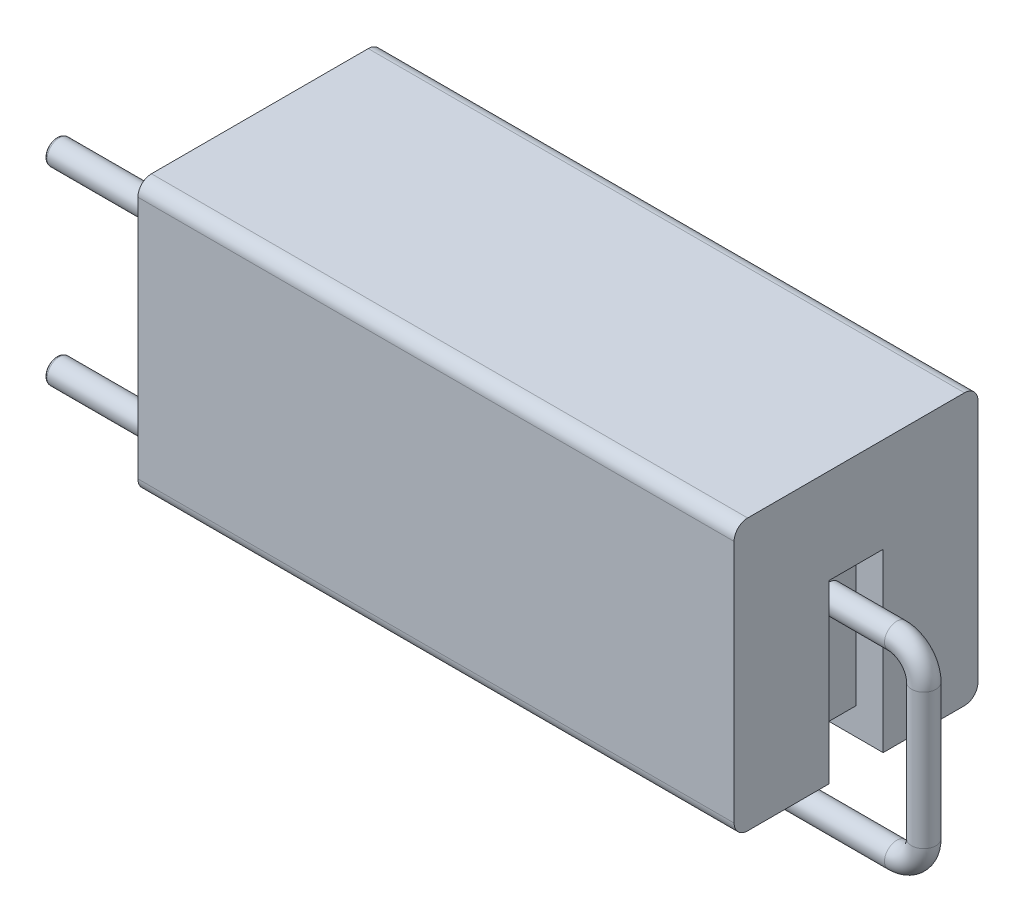
SolidWorks part; units mm, degrees
ref_plane "Front Plane" through (0, 0, 0) normal (0, 0, 1) x (1, 0, 0)
ref_plane "Top Plane" through (0, 0, 0) normal (0, 1, 0) x (1, 0, 0)
ref_plane "Right Plane" through (0, 0, 0) normal (1, 0, 0) x (0, 0, -1)
sketch "Sketch1" plane through (0, 0, 0) normal (0, 0, 1) x (1, 0, 0)
  line L1 (0, 0) -> (22, 0)
  line L2 (0, 0) -> (0, -10)
  line L3 (0, -10) -> (22, -10)
  line L4 (22, 0) -> (22, -10)
  dimension "D1" = 22
  dimension "D2" = 10
extrude "Boss-Extrude1" add sketch "Sketch1" along normal blind 9 contours L1 L4 L3 L2
fillet "Fillet2" radius 0.5 4 edges at (11, 0, 0) (11, -10, 0) (11, -10, 9) (11, 0, 9)
sketch3d "3DSketch1"
  line L1 (22, -10, 8.5) -> (22, -10, 0.5) construction
  line L3 (22, -10, 5.5) -> (22, -3.5, 5.5)
  line L4 (22, -3.5, 5.5) -> (22, -3.5, 3.5)
  line L5 (22, -3.5, 3.5) -> (22, -10, 3.5)
  line L7 (22, -10, 5.5) -> (22, -10, 3.5)
  dimension "D1" = 2
  dimension "D2" = 6.5
sketch "Sketch6" plane through (0, -10, 0) normal (0, -1, 0) x (1, 0, 0)
  line L5 (1, 5.5) -> (1, 3.5)
  line L6 (21, 5.5) -> (21, 3.5)
  line L8 (3, 8) -> (19, 8)
  line L10 (19, 1) -> (3, 1)
  line L13 (3, 8) -> (3, 5.5)
  line L14 (3, 1) -> (3, 3.5)
  line L15 (19, 8) -> (19, 5.5)
  line L16 (19, 1) -> (19, 3.5)
  line L17 (1, 5.5) -> (3, 5.5)
  line L18 (19, 5.5) -> (21, 5.5)
  line L19 (21, 3.5) -> (19, 3.5)
  line L20 (1, 3.5) -> (3, 3.5)
extrude "Cut-Extrude4" cut sketch "3DSketch1" along direction (1, 0, 0) on the side against the normal blind 1 contours L3 L4 L5 L7
sketch "Sketch8" plane through (0, 0, 0) normal (-1, 0, 0) x (0, 0, 1)
  line L0 (5.5, -10) -> (5.5, -3.5)
  line L1 (5.5, -3.5) -> (3.5, -3.5)
  line L2 (3.5, -3.5) -> (3.5, -10)
  line L3 (8.5, -10) -> (0.5, -10) construction
  line L4 (3.5, -10) -> (5.5, -10)
  dimension "D1" = 2
  dimension "D2" = 6.5
extrude "Cut-Extrude5" cut sketch "Sketch8" against normal blind 1
sketch "Sketch9" plane through (0, -10, 0) normal (0, -1, 0) x (1, 0, 0)
extrude "Cut-Extrude6" cut sketch "Sketch6" against normal blind 1
ref_plane "Plane3" through (11, 0, 0) normal (1, 0, 0) x (0, 0, -1)
sketch "Sketch14" plane through (21, 0, 0) normal (1, 0, 0) x (0, 0, -1)
  circle A0 centre (-4.5, -5) radius 0.45
sketch3d "3DSketch5"
  line L0 (21, -5, 4.5) -> (23.5, -5, 4.5)
  line L1 (24.5, -6, 4.5) -> (24.5, -11, 4.5)
  line L2 (23.5, -12, 4.5) -> (-7.5, -12, 4.5)
  arc A0 (23.5, -12, 4.5) -> (24.5, -11, 4.5) centre (23.5, -11, 4.5) ccw
  arc A1 (24.5, -6, 4.5) -> (23.5, -5, 4.5) centre (23.5, -6, 4.5) ccw
  point P9 (24.5, -12, 4.5)
  point P10 (23.5, -11, 5.5)
  point P13 (24.5, -5, 4.5)
  point P14 (23.5, -6, 5.5)
  dimension "D4" = 1
  dimension "D1" = 3.5
  dimension "D2" = 7
  dimension "D3" = 32
sweep "Sweep2" add profiles "Sketch14" path "3DSketch5"
sketch "Sketch15" plane through (1, 0, 0) normal (-1, 0, 0) x (0, 0, 1)
  circle A0 centre (4.5, -5) radius 0.45
sketch3d "3DSketch6"
  line L0 (1, -5, 4.5) -> (-7.5, -5, 4.5)
  dimension "D1" = 8.5
sweep "Sweep3" add profiles "Sketch15" path "3DSketch6"
fillet "Fillet4" radius 0.1 2 edges at (-7.5, -12, 4.05) (-7.5, -5.45, 4.5)
